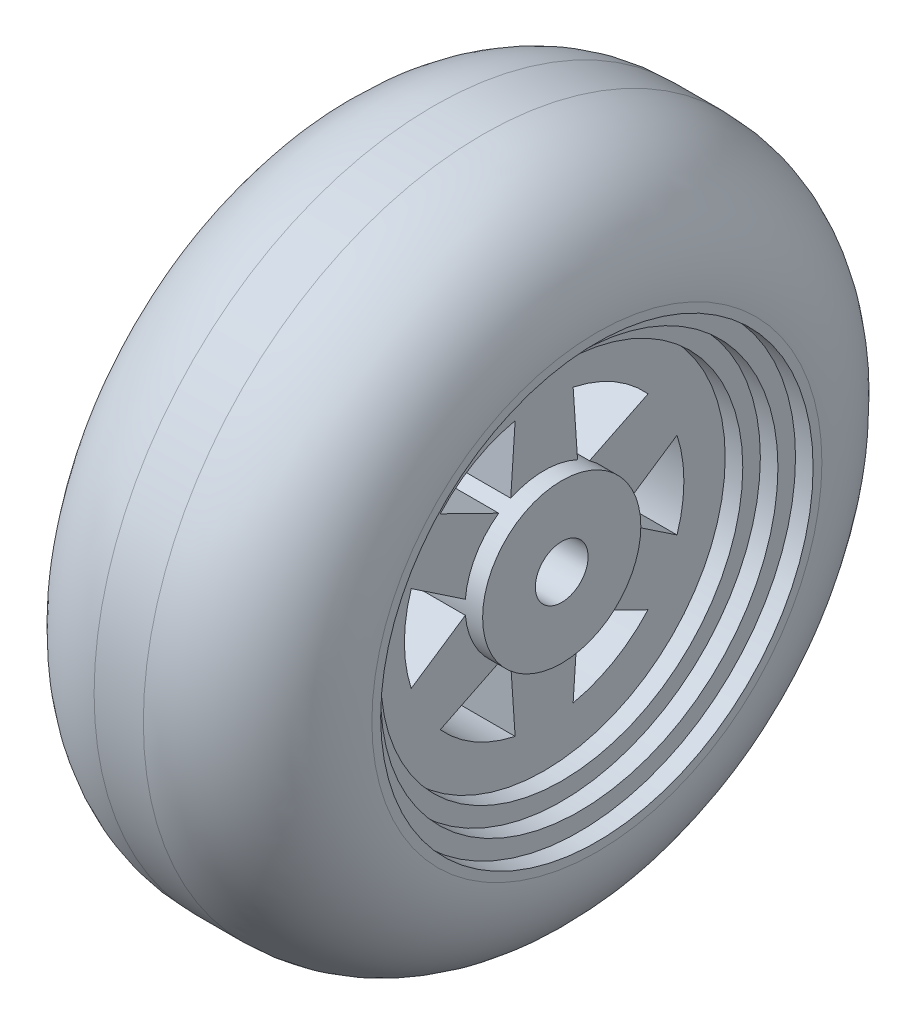
SolidWorks part; units mm, degrees
ref_plane "Plan de face" through (0, 0, 0) normal (0, 0, 1) x (1, 0, 0)
ref_plane "Plan de dessus" through (0, 0, 0) normal (0, 1, 0) x (1, 0, 0)
ref_plane "Plan de droite" through (0, 0, 0) normal (1, 0, 0) x (0, 0, -1)
sketch "Esquisse1" plane through (0, 0, 0) normal (1, 0, 0) x (0, 0, -1)
  line L0 (85.7425, 0) -> (-40.1398, 0) construction
  line L1 (0, -38.596) -> (0, 88.4739) construction
  line L2 (1.9, 4.0792) -> (1.65, 7.7769)
  line L3 (1.9, 5.0499) -> (1.9, 2.7605) construction
  line L4 (1.65, 9.3797) -> (1.65, 7.5881) construction
  line L5 (-1.9, 4.0792) -> (-1.65, 7.7769)
  line L6 (4.4827, 0.3942) -> (7.56, 2.4595)
  line L7 (2.5827, 3.6851) -> (5.91, 5.3174)
  line L8 (2.5827, -3.6851) -> (5.91, -5.3174)
  line L9 (4.4827, -0.3942) -> (7.56, -2.4595)
  line L10 (-1.9, -4.0792) -> (-1.65, -7.7769)
  line L11 (1.9, -4.0792) -> (1.65, -7.7769)
  line L12 (-4.4827, -0.3942) -> (-7.56, -2.4595)
  line L13 (-2.5827, -3.6851) -> (-5.91, -5.3174)
  line L14 (-2.5827, 3.6851) -> (-5.91, 5.3174)
  line L15 (-4.4827, 0.3942) -> (-7.56, 2.4595)
  circle A0 centre (0, 0) radius 19.3
  arc A2 (1.9, -4.0792) -> (2.5827, -3.6851) centre (0, 0) ccw
  arc A3 (1.65, -7.7769) -> (5.91, -5.3174) centre (0, 0) ccw
  arc A4 (4.4827, -0.3942) -> (4.4827, 0.3942) centre (0, 0) ccw
  arc A5 (7.56, -2.4595) -> (7.56, 2.4595) centre (0, 0) ccw
  arc A6 (2.5827, 3.6851) -> (1.9, 4.0792) centre (0, 0) ccw
  arc A7 (5.91, 5.3174) -> (1.65, 7.7769) centre (0, 0) ccw
  arc A8 (-1.9, 4.0792) -> (-2.5827, 3.6851) centre (0, 0) ccw
  arc A9 (-1.65, 7.7769) -> (-5.91, 5.3174) centre (0, 0) ccw
  arc A10 (-4.4827, 0.3942) -> (-4.4827, -0.3942) centre (0, 0) ccw
  arc A11 (-7.56, 2.4595) -> (-7.56, -2.4595) centre (0, 0) ccw
  arc A12 (-2.5827, -3.6851) -> (-1.9, -4.0792) centre (0, 0) ccw
  arc A13 (-5.91, -5.3174) -> (-1.65, -7.7769) centre (0, 0) ccw
  dimension "D1" = 1.65
  dimension "D2" = 1.9
extrude "Extrusion1" add sketch "Esquisse1" along normal blind 15.8
sketch "Esquisse2" plane through (15.8, 0, 0) normal (1, 0, 0) x (0, 0, -1)
  circle A0 centre (0, 0) radius 12.3
extrude "Enlèv. mat.-Extru.1" cut sketch "Esquisse2" against normal blind 1
sketch "Esquisse3" plane through (14.8, 0, 0) normal (1, 0, 0) x (0, 0, -1)
  circle A0 centre (0, 0) radius 11.3
extrude "Enlèv. mat.-Extru.2" cut sketch "Esquisse3" against normal blind 1
sketch "Esquisse4" plane through (13.8, 0, 0) normal (1, 0, 0) x (0, 0, -1)
  circle A0 centre (0, 0) radius 10.3
extrude "Enlèv. mat.-Extru.3" cut sketch "Esquisse4" against normal blind 1
sketch "Esquisse6" plane through (0, 0, 0) normal (-1, 0, 0) x (0, 0, 1)
  circle A0 centre (0, 0) radius 12.3
extrude "Enlèv. mat.-Extru.4" cut sketch "Esquisse6" against normal blind 1
sketch "Esquisse7" plane through (1, 0, 0) normal (-1, 0, 0) x (0, 0, 1)
  circle A0 centre (0, 0) radius 4.5
extrude "Extrusion3" add sketch "Esquisse7" along normal blind 5
sketch "Esquisse8" plane through (12.8, 0, 0) normal (1, 0, 0) x (0, 0, -1)
  circle A0 centre (0, 0) radius 4.5
extrude "Extrusion4" add sketch "Esquisse8" along normal blind 1
sketch "Esquisse9" plane through (13.8, 0, 0) normal (1, 0, 0) x (0, 0, -1)
  circle A0 centre (0, 0) radius 1.5
extrude "Enlèv. mat.-Extru.5" cut sketch "Esquisse9" against normal through all
fillet "Congé1" radius 6.5 2 edges at (0, 0, -19.3) (15.8, 0, -19.3)
